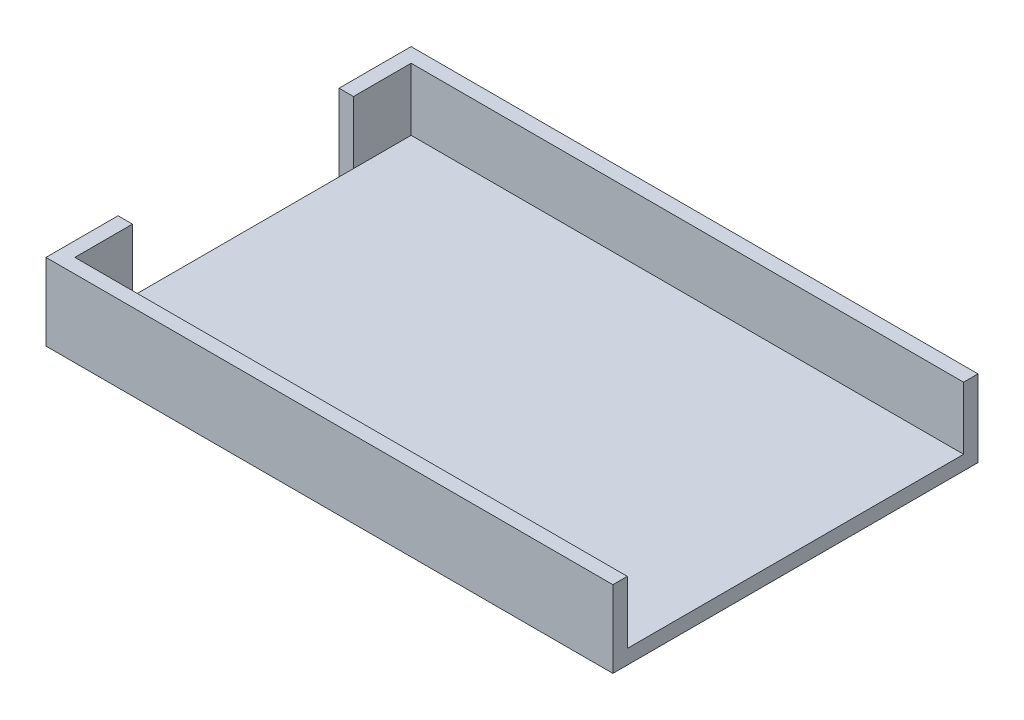
SolidWorks part; units mm, degrees
ref_plane "Front Plane" through (0, 0, 0) normal (0, 0, 1) x (1, 0, 0)
ref_plane "Top Plane" through (0, 0, 0) normal (0, 1, 0) x (1, 0, 0)
ref_plane "Right Plane" through (0, 0, 0) normal (1, 0, 0) x (0, 0, -1)
sketch "Sketch1" plane through (0, 0, 0) normal (0, 1, 0) x (1, 0, 0)
  line L1 (-81.5856, 39.8469) -> (100.9769, 39.8469)
  line L2 (-81.5856, 39.8469) -> (-81.5856, -71.2781)
  line L3 (-81.5856, -71.2781) -> (100.9769, -71.2781)
  line L4 (100.9769, 39.8469) -> (100.9769, -71.2781)
  point P6 (0, 0)
extrude "Boss-Extrude1" add sketch "Sketch1" along normal blind 4.7625
sketch "Sketch3" plane through (0, 0, 0) normal (0, -1, 0) x (1, 0, 0)
  line L1 (-86.3481, -39.8469) -> (-86.3481, -20.7969)
  line L2 (-86.3481, 71.2781) -> (-86.3481, 52.2281)
  line L3 (-86.3481, 52.2281) -> (-81.5856, 52.2281)
  line L4 (-81.5856, -39.8469) -> (-81.5856, 71.2781) construction
  line L5 (-81.5856, 52.2281) -> (-81.5856, 71.2781)
  line L6 (-86.3481, 71.2781) -> (-86.3481, 76.0406)
  line L7 (-86.3481, 76.0406) -> (-81.5856, 76.0406)
  line L8 (-81.5856, 76.0406) -> (100.9769, 76.0406)
  line L9 (100.9769, 71.2781) -> (100.9769, 76.0406)
  line L10 (-81.5856, 71.2781) -> (100.9769, 71.2781)
  line L11 (-86.3481, -20.7969) -> (-81.5856, -20.7969)
  line L12 (-81.5856, -20.7969) -> (-81.5856, -39.8469)
  line L13 (100.9769, -39.8469) -> (-81.5856, -39.8469)
  line L14 (-86.3481, -39.8469) -> (-86.3481, -44.6094)
  line L15 (-86.3481, -44.6094) -> (100.9769, -44.6094)
  line L16 (100.9769, -44.6094) -> (100.9769, -39.8469)
extrude "Boss-Extrude2" add sketch "Sketch3" against normal blind 25.4
